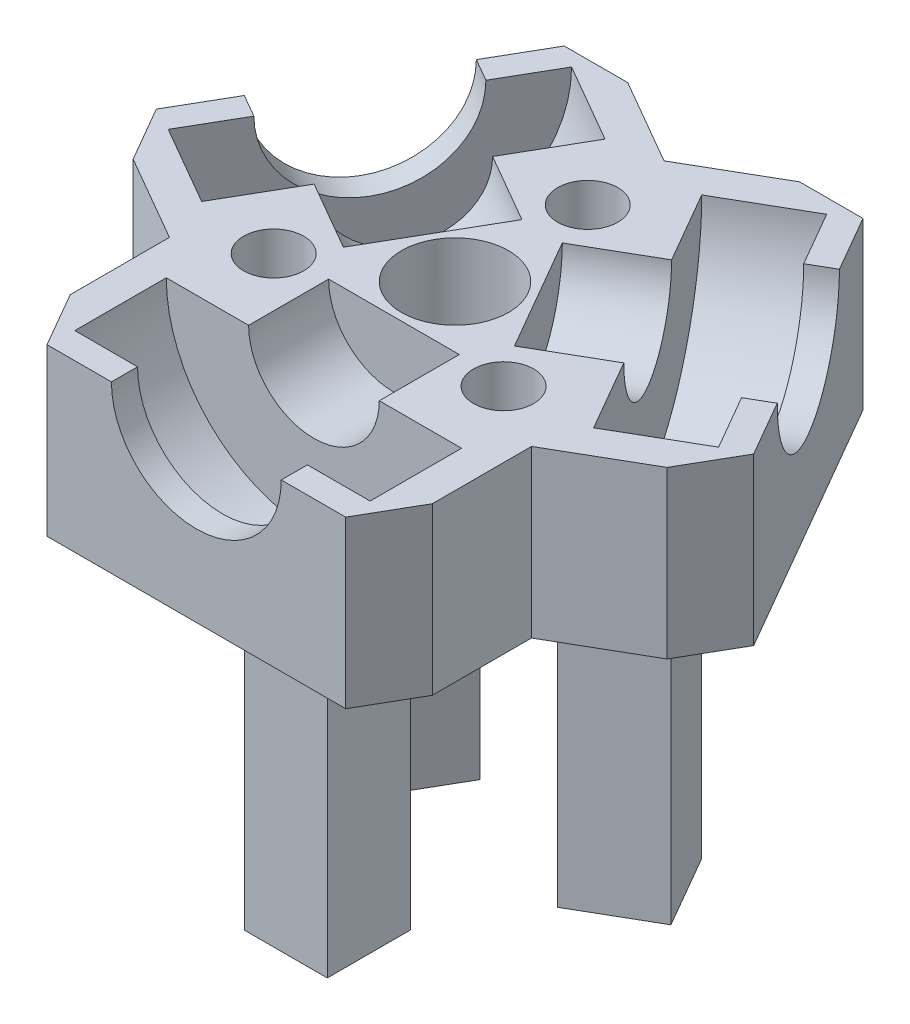
SolidWorks part; units mm, degrees
ref_plane "Front Plane" through (0, 0, 0) normal (0, 0, 1) x (1, 0, 0)
ref_plane "Top Plane" through (0, 0, 0) normal (0, 1, 0) x (1, 0, 0)
ref_plane "Right Plane" through (0, 0, 0) normal (1, 0, 0) x (0, 0, -1)
sketch "Sketch1" plane through (0, 0, 0) normal (0, 1, 0) x (1, 0, 0)
  line L1 (11.43, -19.7973) -> (22.86, 0)
  line L2 (22.86, 0) -> (11.43, 19.7973)
  line L3 (11.43, 19.7973) -> (-11.43, 19.7973)
  line L4 (-11.43, 19.7973) -> (-22.86, 0)
  line L5 (-22.86, 0) -> (-11.43, -19.7973)
  line L6 (-11.43, -19.7973) -> (11.43, -19.7973)
  circle A0 centre (0, 0) radius 19.7973 construction
  dimension "D1" = 22.86
extrude "Boss-Extrude1" add sketch "Sketch1" along normal blind 12.7 contours L4 L5 L6 L1 L2 L3
sketch "Sketch2" plane through (0, 0, 0) normal (0, -1, 0) x (1, 0, 0)
  circle A0 centre (0, 0) radius 4.1
  circle A1 centre (0, 0) radius 7.1
  dimension "D1" = 8.2
  dimension "D2" = 3
extrude "Boss-Extrude2" add sketch "Sketch2" along normal blind 3.5
sketch "Sketch4" plane through (0, 0, 0) normal (0, -1, 0) x (1, 0, 0)
  line L0 (12.8025, -3.7254) -> (7.3033, -0.5504)
  line L1 (-3.175, 12.95) -> (3.175, 12.95)
  line L2 (-3.175, 12.95) -> (-3.175, 6.6)
  line L3 (-3.175, 6.6) -> (3.175, 6.6)
  line L4 (3.175, 12.95) -> (3.175, 6.6)
  line L5 (-3.175, 12.95) -> (3.175, 6.6) construction
  line L6 (-3.175, 6.6) -> (3.175, 12.95) construction
  line L7 (12.8025, -3.7254) -> (9.6275, -9.2246)
  line L8 (9.6275, -9.2246) -> (4.1283, -6.0496)
  line L9 (7.3033, -0.5504) -> (4.1283, -6.0496)
  line L10 (-9.6275, -9.2246) -> (-4.1283, -6.0496)
  line L11 (-9.6275, -9.2246) -> (-12.8025, -3.7254)
  line L12 (-12.8025, -3.7254) -> (-7.3033, -0.5504)
  line L13 (-4.1283, -6.0496) -> (-7.3033, -0.5504)
  circle A1 centre (0, 0) radius 4.1 construction
  circle A2 centre (0, 0) radius 4.1 construction
  point P0 (0, 9.775)
  point P18 (0, 0)
  dimension "D1" = 6.35
  dimension "D2" = 2.5
  dimension "D4" = 2.5
  dimension "D5" = 2.5
  dimension "D3" = 3
extrude "Boss-Extrude4" add sketch "Sketch4" along normal blind 25.4
sketch "Sketch5" plane through (0, 12.7, 0) normal (0, 1, 0) x (1, 0, 0)
  line L14 (0, -19.7973) -> (0, -4.6723)
  line L15 (-11.43, -19.7973) -> (11.43, -19.7973) construction
  line L16 (0, -4.6723) -> (-5, -4.6723)
  line L17 (-5, -4.6723) -> (-5, -10.7973)
  line L18 (-5, -10.7973) -> (-11.3, -10.7973)
  line L19 (-11.3, -10.7973) -> (-11.3, -17.7973)
  line L20 (-11.3, -17.7973) -> (-6.5, -17.7973)
  line L21 (-6.5, -17.7973) -> (-6.5, -19.7973)
  line L22 (-6.5, -19.7973) -> (0, -19.7973)
  dimension "D1" = 6.5
  dimension "D2" = 11.3
  dimension "D3" = 2
  dimension "D4" = 7
  dimension "D5" = 6.125
  dimension "D6" = 5
revolve "Cut-Revolve1" cut sketch "Sketch5" angle 360 about L14
pattern_circular "CirPattern1" count 3 over 360 about axis through (0, 0, 0) along (0, 1, 0) of "Cut-Revolve1"
sketch "Sketch6" plane through (0, 12.7, 0) normal (0, 1, 0) x (1, 0, 0)
  circle A0 centre (0, 0) radius 4.1
  dimension "D1" = 8.2
extrude "Cut-Extrude1" cut sketch "Sketch6" against normal through all
sketch "Sketch7" plane through (0, 12.7, 0) normal (0, 1, 0) x (1, 0, 0)
  circle A0 centre (0, 10.16) radius 2.3
  circle A1 centre (8.7988, -5.08) radius 2.3
  circle A2 centre (-8.7988, -5.08) radius 2.3
  circle A3 centre (0, 0) radius 10.16 construction
  point P11 (0, 0)
  dimension "D1" = 4.6
  dimension "D2" = 20.32
  dimension "D3" = 3
extrude "Cut-Extrude2" cut sketch "Sketch7" against normal blind 5.7
sketch "Sketch8" plane through (0, 0, 0) normal (0, -1, 0) x (1, 0, 0)
  line L0 (-22.86, 0) -> (-7.0264, 4.0567)
  line L1 (-7.0264, 4.0567) -> (-11.43, 19.7973)
  line L2 (-11.43, 19.7973) -> (-22.86, 0)
  line L3 (11.43, 19.7973) -> (7.0264, 4.0567)
  line L4 (7.0264, 4.0567) -> (22.86, 0)
  line L5 (22.86, 0) -> (11.43, 19.7973)
  line L6 (11.43, -19.7973) -> (0, -8.1133)
  line L7 (0, -8.1133) -> (-11.43, -19.7973)
  line L8 (-11.43, -19.7973) -> (11.43, -19.7973)
  line L9 (22.86, 0) -> (11.43, -19.7973) construction
  point P13 (0, 0)
  dimension "D1" = 11.684
  dimension "D2" = 3
extrude "Cut-Extrude3" [suppressed] cut sketch "Sketch8" against normal blind 4.572
sketch "Sketch9" plane through (0, 12.7, 0) normal (0, 1, 0) x (1, 0, 0)
  line L0 (-6.5772, 19.7973) -> (0, 16)
  line L1 (11.43, 19.7973) -> (-11.43, 19.7973) construction
  line L2 (20.4336, -4.2027) -> (13.8564, -8)
  line L3 (0, 16) -> (6.5772, 19.7973)
  line L4 (13.8564, -8) -> (13.8564, -15.5947)
  line L5 (6.5772, 19.7973) -> (-6.5772, 19.7973)
  line L6 (13.8564, -15.5947) -> (20.4336, -4.2027)
  line L7 (-13.8564, -15.5947) -> (-13.8564, -8)
  line L8 (-13.8564, -8) -> (-20.4336, -4.2027)
  line L9 (-20.4336, -4.2027) -> (-13.8564, -15.5947)
  point P6 (0, 19.7973)
  point P7 (0, 19.7973)
  point P15 (0, 0)
  dimension "D1" = 3.7973
  dimension "D2" = 13.1544
  dimension "D3" = 3
extrude "Cut-Extrude4" cut sketch "Sketch9" against normal through all
